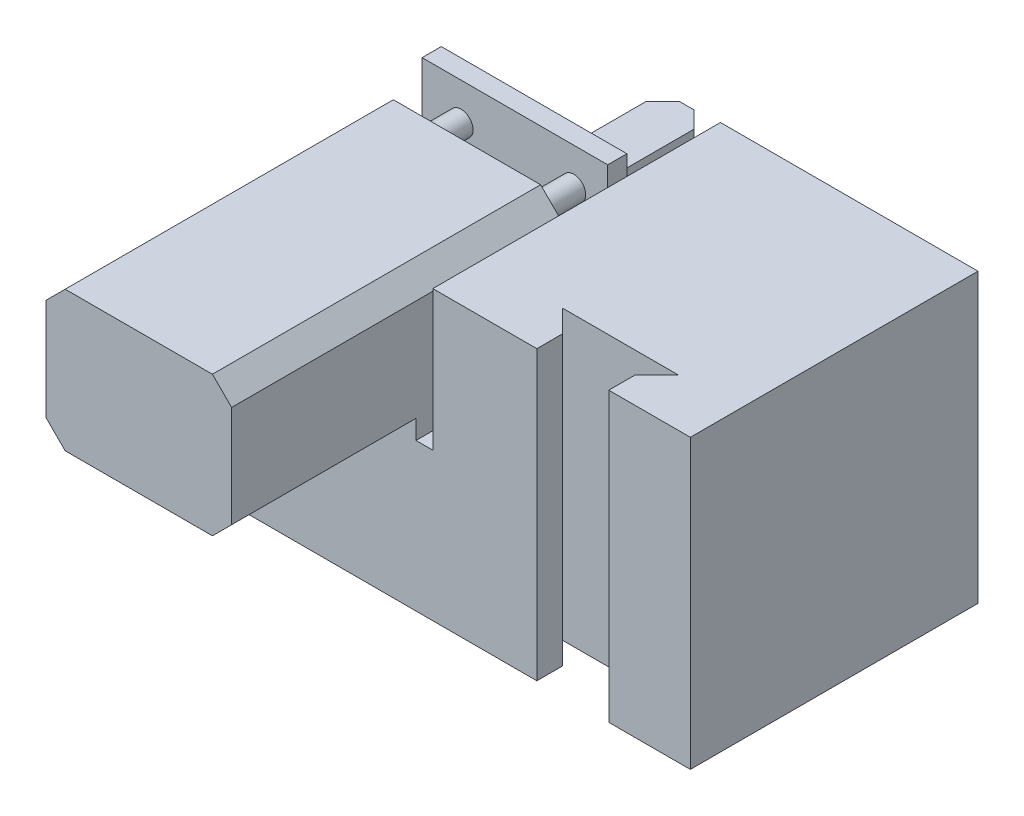
SolidWorks part; units mm, degrees
ref_plane "Front Plane" through (0, 0, 0) normal (0, 0, 1) x (1, 0, 0)
ref_plane "Top Plane" through (0, 0, 0) normal (0, 1, 0) x (1, 0, 0)
ref_plane "Right Plane" through (0, 0, 0) normal (1, 0, 0) x (0, 0, -1)
sketch "Sketch1" plane through (0, 0, 0) normal (0, 1, 0) x (1, 0, 0)
  line L1 (0, 0) -> (127, 0)
  line L2 (0, 0) -> (0, 76.2)
  line L3 (0, 76.2) -> (127, 76.2)
  line L4 (127, 0) -> (127, 76.2)
  dimension "D1" = 127
  dimension "D2" = 76.2
extrude "Boss-Extrude1" add sketch "Sketch1" along normal blind 76.2
sketch "Sketch2" plane through (0, 76.2, 0) normal (0, 1, 0) x (1, 0, 0)
  line L0 (86.341, 0) -> (105.391, 0)
  line L1 (105.391, 0) -> (105.391, 6.858)
  line L2 (105.391, 6.858) -> (111.233, 12.7)
  line L3 (111.233, 12.7) -> (80.499, 12.7)
  line L4 (80.499, 12.7) -> (86.341, 6.858)
  line L5 (86.341, 6.858) -> (86.341, 0)
  line L6 (0, 0) -> (127, 0) construction
  dimension "D1" = 0
  dimension "D2" = 6.858
  dimension "D3" = 6.858
  dimension "D4" = 30.734
extrude "Cut-Extrude1" cut sketch "Sketch2" against normal through all
sketch "Sketch3" plane through (0, 0, -76.2) normal (0, 0, -1) x (-1, 0, 0)
  line L1 (0, 76.2) -> (-58.7764, 76.2)
  line L2 (0, 76.2) -> (0, 39.1255)
  line L3 (0, 39.1255) -> (-58.7764, 39.1255)
  line L4 (-58.7764, 76.2) -> (-58.7764, 39.1255)
extrude "Cut-Extrude2" cut sketch "Sketch3" against normal through all
sketch "Sketch4" plane through (0, 39.1255, 0) normal (0, 1, 0) x (1, 0, 0)
  line L1 (54.3162, 38.1) -> (5.1489, 38.1)
  line L2 (54.3162, 38.1) -> (54.3162, -48.8315)
  line L3 (54.3162, -48.8315) -> (5.1489, -48.8315)
  line L4 (5.1489, 38.1) -> (5.1489, -48.8315)
extrude "Boss-Extrude3" add sketch "Sketch4" along normal up to surface (37.0745 mm away) up to face at (94.6749, 76.2, -19.1516)
chamfer "Chamfer1" distance 5.08 angle 45 4 edges at (54.3162, 39.1255, 24.4157) (5.1489, 39.1255, 24.4157) (54.3162, 76.2, 5.3657) (5.1489, 76.2, 5.3657)
sketch "Sketch5" plane through (0, 0, -38.1) normal (0, 0, -1) x (-1, 0, 0)
  circle A0 centre (-45.3124, 67.1353) radius 3.175
  circle A1 centre (-15.472, 67.1353) radius 3.175
  circle A2 centre (-45.3124, 45.4486) radius 3.175
  circle A3 centre (-15.472, 45.4486) radius 3.175
  point P2 (0, 0)
  point P3 (-45.3124, 67.1353)
  point P6 (-15.472, 67.1353)
  point P9 (-45.3124, 45.4486)
  point P12 (-15.472, 45.4486)
  dimension "D1" = 6.35
extrude "Boss-Extrude4" add sketch "Sketch5" along normal blind 12.7 contours A3 | A2 | A0 | A1
sketch "Sketch6" plane through (0, 0, -50.8) normal (0, 0, -1) x (-1, 0, 0)
  line L0 (-58.7764, 39.1255) -> (0, 39.1255) construction
  line L1 (-54.3162, 76.9672) -> (-5.1489, 76.9672)
  line L2 (-54.3162, 76.9672) -> (-54.3162, 39.1255)
  line L3 (-54.3162, 39.1255) -> (-5.1489, 39.1255)
  line L4 (-5.1489, 76.9672) -> (-5.1489, 39.1255)
  line L5 (-5.1489, 71.12) -> (-5.1489, 39.1255) construction
extrude "Boss-Extrude5" add sketch "Sketch6" along normal blind 5.08
sketch "Sketch7" plane through (0, 0, -55.88) normal (0, 0, -1) x (-1, 0, 0)
  line L0 (-54.3162, 76.9672) -> (-54.3162, 39.1255) construction
  line L6 (-46.366, 45.1147) -> (-33.666, 45.1147)
  line L7 (-46.366, 45.1147) -> (-46.366, 41.1575)
  line L8 (-46.366, 41.1575) -> (-33.666, 41.1575)
  line L9 (-33.666, 45.1147) -> (-33.666, 41.1575)
  line L13 (-25.7158, 45.1147) -> (-13.0158, 45.1147)
  line L14 (-25.7158, 45.1147) -> (-25.7158, 41.1575)
  line L15 (-25.7158, 41.1575) -> (-13.0158, 41.1575)
  line L16 (-13.0158, 45.1147) -> (-13.0158, 41.1575)
  line L18 (-54.3162, 39.1255) -> (-5.1489, 39.1255) construction
  dimension "D1" = 12.7
  dimension "D2" = 12.7
  dimension "D3" = 7.9502
  dimension "D4" = 7.9502
  dimension "D5" = 2.032
  dimension "D6" = 2.032
extrude "Boss-Extrude6" add sketch "Sketch7" along normal blind 50.8
chamfer "Chamfer2" distance 4.445 angle 45 4 edges at (46.366, 43.1361, -106.68) (25.7158, 43.1361, -106.68) (33.666, 43.1361, -106.68) (13.0158, 43.1361, -106.68)
